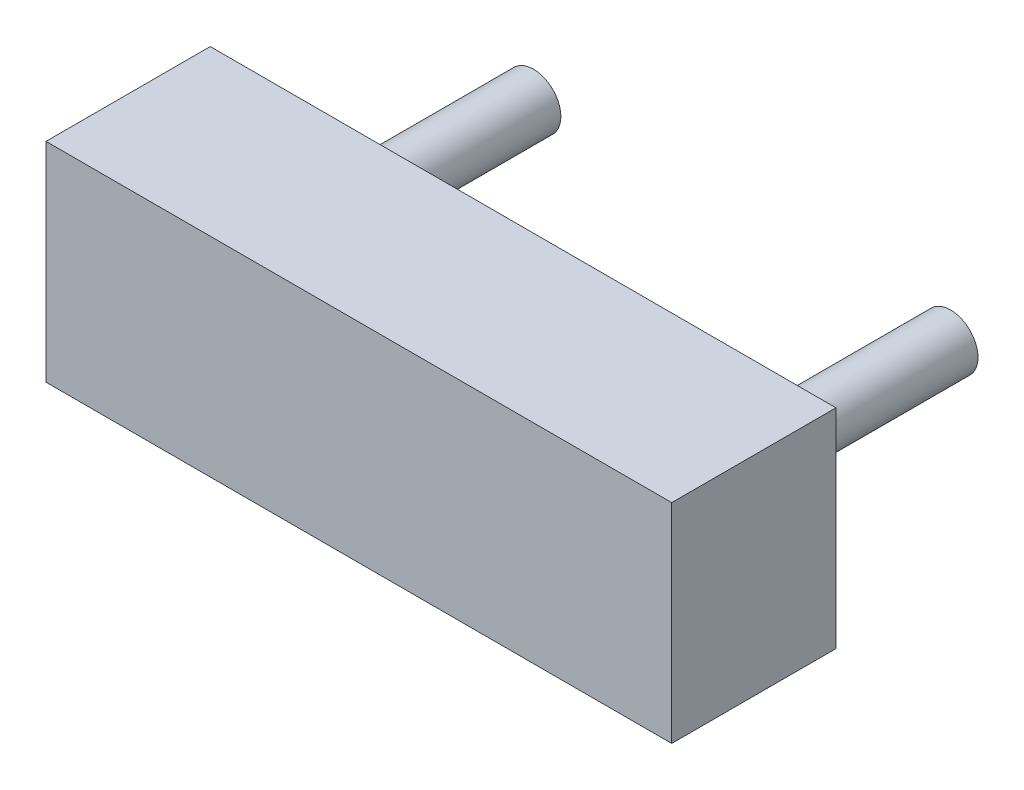
SolidWorks part; units mm, degrees
ref_plane "Front Plane" through (0, 0, 0) normal (0, 0, 1) x (1, 0, 0)
ref_plane "Top Plane" through (0, 0, 0) normal (0, 1, 0) x (1, 0, 0)
ref_plane "Right Plane" through (0, 0, 0) normal (1, 0, 0) x (0, 0, -1)
sketch "Sketch1" plane through (0, 0, 0) normal (0, 0, 1) x (1, 0, 0)
  line L0 (-2.8575, 0.9525) -> (-2.8575, -0.9525)
  line L1 (-2.8575, -0.9525) -> (2.8575, -0.9525)
  line L2 (2.8575, -0.9525) -> (2.8575, 0.9525)
  line L3 (2.8575, 0.9525) -> (-2.8575, 0.9525)
extrude "Component_Outline" add sketch "Sketch1" along normal blind 1.5 separate body
sketch "Sketch2" plane through (0, 0, 0) normal (0, 0, 1) x (1, 0, 0)
  circle A0 centre (-1.905, 0) radius 0.25
extrude "1" add sketch "Sketch2" against normal blind 2 separate body
sketch "Sketch3" plane through (0, 0, 0) normal (0, 0, 1) x (1, 0, 0)
  circle A0 centre (1.905, 0) radius 0.25
extrude "2" add sketch "Sketch3" against normal blind 2 separate body
sketch3d "3DSketch1"
  line L0 (0, 0, 0) -> (1, 0, 0)
  line L1 (0, 0, 0) -> (0, 1, 0)
  line L2 (0, 0, 0) -> (0, 0, 1)
  point P0 (0, 0, 0)
